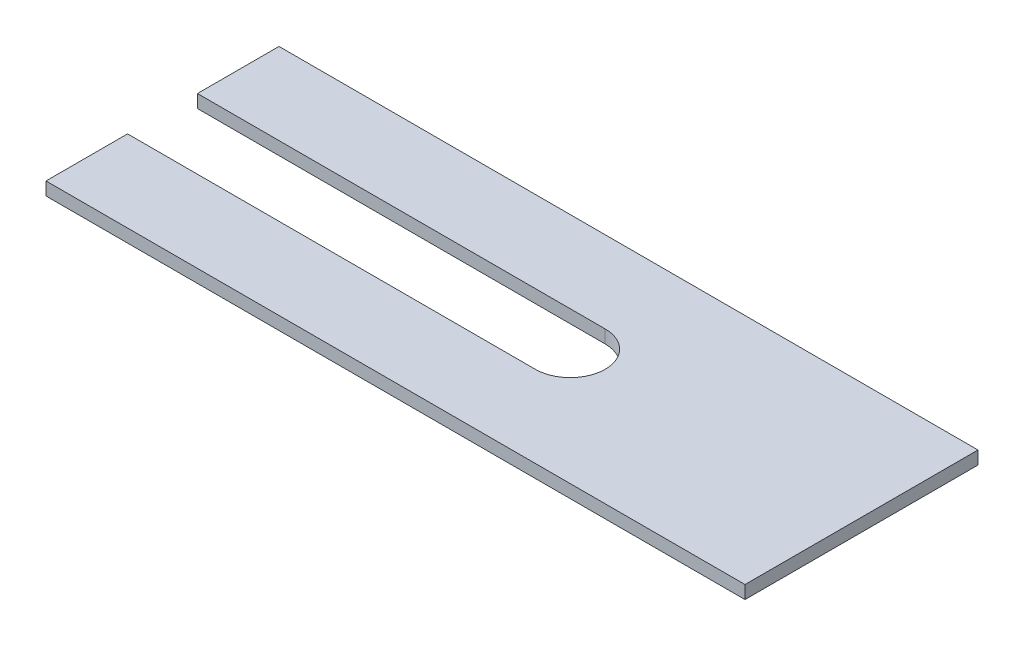
SolidWorks part; units mm, degrees
ref_plane "Front Plane" through (0, 0, 0) normal (0, 0, 1) x (1, 0, 0)
ref_plane "Top Plane" through (0, 0, 0) normal (0, 1, 0) x (1, 0, 0)
ref_plane "Right Plane" through (0, 0, 0) normal (1, 0, 0) x (0, 0, -1)
sketch "Sketch1" plane through (0, 0, 0) normal (0, 1, 0) x (1, 0, 0)
  line L0 (17.5, 0) -> (-17.5, 0) construction
  line L3 (17.5, -3) -> (-17.5, -3)
  line L4 (17.5, 3) -> (-17.5, 3)
  line L6 (-17.5, -10) -> (42.5, -10)
  line L7 (-17.5, -10) -> (-17.5, 10)
  line L8 (-17.5, 10) -> (42.5, 10)
  line L9 (42.5, -10) -> (42.5, 10)
  line L10 (12.5, 10) -> (12.5, -10) construction
  line L11 (-17.5, 0) -> (42.5, 0) construction
  arc A2 (17.5, -3) -> (17.5, 3) centre (17.5, 0) ccw
  arc A3 (-17.5, 3) -> (-17.5, -3) centre (-17.5, 0) ccw
  point P2 (-19.2417, 0)
  point P3 (0, 0)
  point P13 (6.2559, 0)
  point P257 (12.5, 0)
  dimension "D1" = 20
  dimension "D2" = 60
  dimension "D3" = 6
  dimension "D4" = 35
extrude "Boss-Extrude1" add sketch "Sketch1" along normal blind 1.62 contours A2 L3 L7 L6 L9 L8 L4
chamfer "Chamfer1" distance 0.5 angle 45 8 edges at (0, 0, 3) (-17.5, 0, 6.5) (12.5, 0, 10) (42.5, 0, 0) (12.5, 0, -10) (-17.5, 0, -6.5) (0, 0, -3) (20.5, 0, 0)
